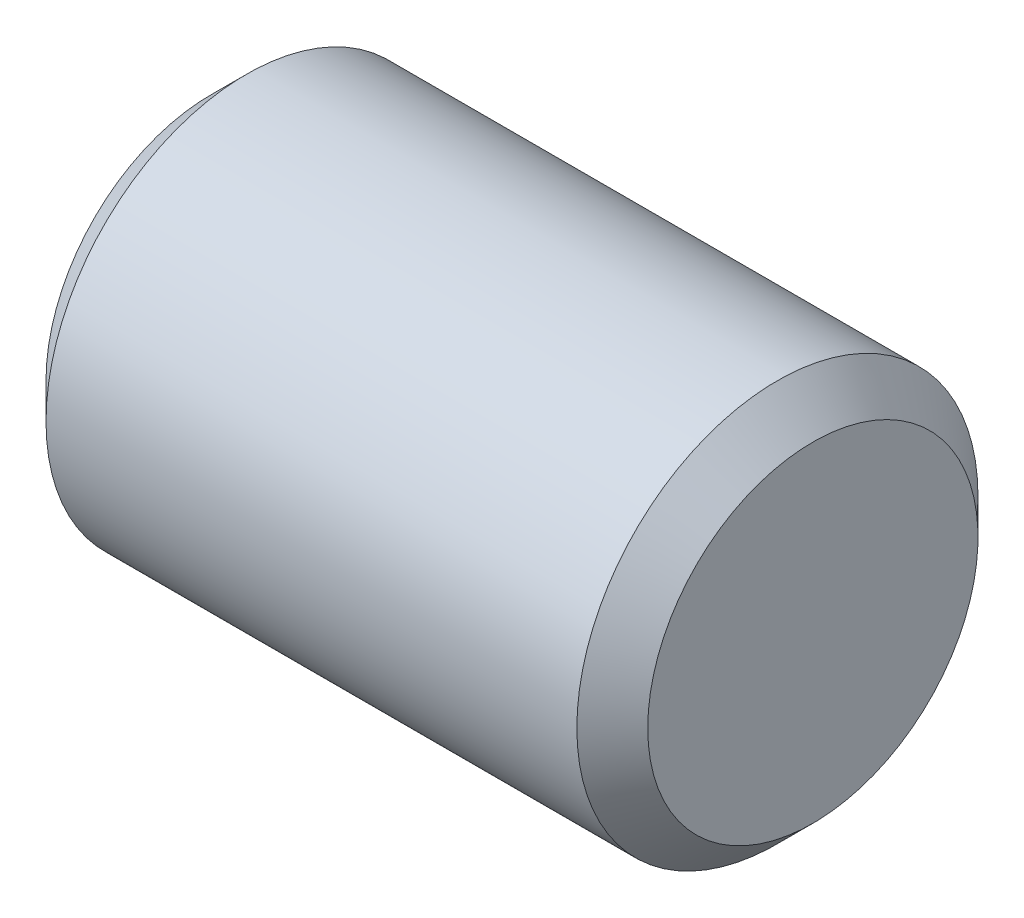
SolidWorks part; units mm, degrees
ref_plane "Front Plane" through (0, 0, 0) normal (0, 0, 1) x (1, 0, 0)
ref_plane "Top Plane" through (0, 0, 0) normal (0, 1, 0) x (1, 0, 0)
ref_plane "Right Plane" through (0, 0, 0) normal (1, 0, 0) x (0, 0, -1)
sketch "Sketch1" plane through (0, 0, 0) normal (0, 0, 1) x (1, 0, 0)
  line L0 (-4.9652, 0) -> (4.9652, 0) construction
  line L1 (-2.8636, 0) -> (-2.8636, -1.6464)
  line L2 (-2.5101, -2) -> (2.7828, -2)
  line L3 (3.1364, -1.6464) -> (3.1364, 0)
  line L4 (-2.8636, 0) -> (3.1364, 0)
  line L5 (-2.8636, -1.6464) -> (-2.5101, -2)
  line L6 (3.1364, -1.6464) -> (2.7828, -2)
  point P4 (0, 0)
  dimension "D3" = 45
  dimension "D4" = 0.5
revolve "Revolve1" add sketch "Sketch1" angle 360 about L0
